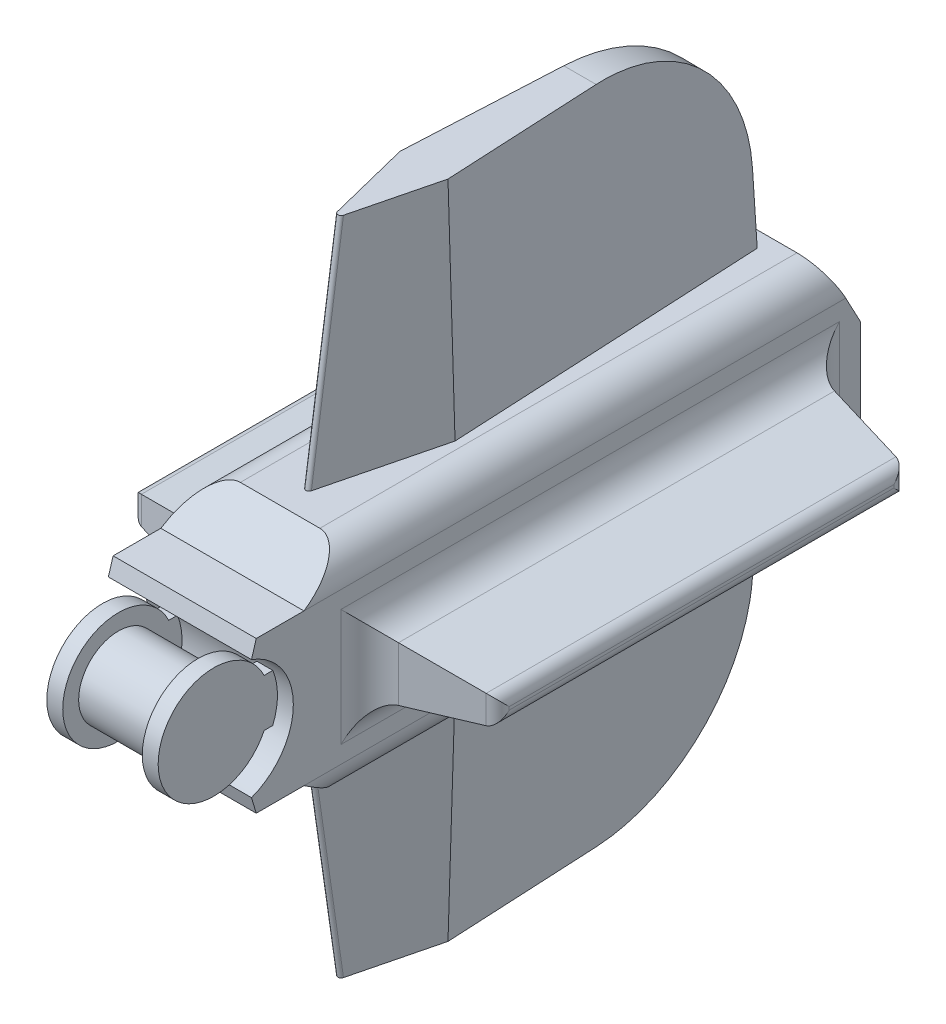
SolidWorks part; units mm, degrees
ref_plane "Front Plane" through (0, 0, 0) normal (0, 0, 1) x (1, 0, 0)
ref_plane "Top Plane" through (0, 0, 0) normal (0, 1, 0) x (1, 0, 0)
ref_plane "Right Plane" through (0, 0, 0) normal (1, 0, 0) x (0, 0, -1)
sketch "Sketch1" plane through (0, 0, 0) normal (1, 0, 0) x (0, 0, -1)
  circle A0 centre (0, 0) radius 3.175
  dimension "D1" = 6.35
extrude "Boss-Extrude1" add sketch "Sketch1" along normal mid plane 6.35
sketch "Sketch2" plane through (3.175, 0, 0) normal (1, 0, 0) x (0, 0, -1)
  circle A0 centre (0, 0) radius 4.445
  dimension "D1" = 8.89
extrude "Boss-Extrude2" add sketch "Sketch2" along normal blind 1.27
mirror "Mirror1" about plane through (0, 0, 0) normal (1, 0, 0) of "Boss-Extrude2"
sketch "Sketch3" plane through (4.445, 0, 0) normal (1, 0, 0) x (0, 0, -1)
  line L1 (0, 1.905) -> (6.35, 1.905)
  line L2 (0, 1.905) -> (0, -1.905)
  line L3 (0, -1.905) -> (6.35, -1.905)
  line L4 (6.35, 1.905) -> (6.35, -1.905)
  point P4 (0, 0)
  dimension "D1" = 3.81
  dimension "D2" = 6.35
extrude "Boss-Extrude3" add sketch "Sketch3" against normal blind 1.27
mirror "Mirror2" about plane through (0, 0, 0) normal (1, 0, 0) of "Boss-Extrude3"
sketch "Sketch4" plane through (-3.175, 0, 0) normal (1, 0, 0) x (0, 0, -1)
  line L0 (1.7375, 4.7736) -> (0, 0) construction
  line L1 (0, 0) -> (5.08, 0) construction
  line L2 (1.7375, 4.7736) -> (2.1185, 6.0436)
  line L3 (2.1185, 6.0436) -> (5.9285, 6.0436)
  line L4 (0, 0) -> (1.7375, -4.7736) construction
  line L5 (5.9285, 6.0436) -> (9.7385, 8.5836)
  line L6 (9.7385, 8.5836) -> (47.8385, 8.5836)
  line L7 (47.8385, 8.5836) -> (50.3785, 3.81)
  line L8 (50.3785, 3.81) -> (50.3785, -3.81)
  line L9 (50.3785, 0) -> (5.08, 0) construction
  line L10 (47.8385, -8.5836) -> (50.3785, -3.81)
  line L11 (9.7385, -8.5836) -> (47.8385, -8.5836)
  line L12 (5.9285, -6.0436) -> (9.7385, -8.5836)
  line L13 (2.1185, -6.0436) -> (5.9285, -6.0436)
  line L14 (1.7375, -4.7736) -> (2.1185, -6.0436)
  arc A0 (1.7375, 4.7736) -> (1.7375, -4.7736) centre (0, 0) cw
  dimension "D1" = 5.08
  dimension "D2" = 140
  dimension "D3" = 1.27
  dimension "D4" = 0.381
  dimension "D5" = 3.81
  dimension "D6" = 3.81
  dimension "D7" = 2.54
  dimension "D8" = 38.1
  dimension "D9" = 7.62
  dimension "D10" = 2.54
extrude "Boss-Extrude4" add sketch "Sketch4" against normal blind 2.54 and the other way blind 8.89
sketch "Sketch5" plane through (0, 0, -50.3785) normal (0, 0, -1) x (-1, 0, 0)
  circle A0 centre (0, 0) radius 3.175
  dimension "D1" = 6.35
extrude "Cut-Extrude1" cut sketch "Sketch5" against normal blind 12.7
fillet "Fillet1" radius 2.54 4 edges at (5.715, -8.5836, -28.7885) (-5.715, -8.5836, -28.7885) (-5.715, 8.5836, -28.7885) (5.715, 8.5836, -28.7885)
sketch "Sketch6" plane through (5.715, 0, 0) normal (1, 0, 0) x (0, 0, -1)
  line L0 (50.3785, -3.81) -> (50.3785, 3.81) construction
  line L1 (11.0085, 2.54) -> (46.5685, 2.54)
  line L2 (11.0085, 2.54) -> (11.0085, -2.54)
  line L3 (11.0085, -2.54) -> (46.5685, -2.54)
  line L4 (46.5685, 2.54) -> (46.5685, -2.54)
  point P4 (11.0085, 0)
  point P6 (50.3785, 0)
  dimension "D1" = 3.81
  dimension "D2" = 5.08
  dimension "D3" = 35.56
extrude "Boss-Extrude5" add sketch "Sketch6" along normal blind 8.89 draft 10
mirror "Mirror3" about plane through (0, 0, 0) normal (1, 0, 0) of "Boss-Extrude5"
fillet "Fillet2" radius 1.016 8 edges at (-14.605, -0.9725, -28.7885) (-14.605, 0, -45.0009) (-14.605, 0.9725, -28.7885) (-14.605, 0, -12.576) (14.605, 0.9725, -28.7885) (14.605, 0, -45.0009) (14.605, -0.9725, -28.7885) (14.605, 0, -12.576)
fillet "Fillet3" radius 2.54 8 edges at (5.715, -2.54, -28.7885) (5.715, 0, -11.0085) (5.715, 0, -46.5685) (5.715, 2.54, -28.7885) (-5.715, 0, -11.0085) (-5.715, 0, -46.5685) (-5.715, -2.54, -28.7885) (-5.715, 2.54, -28.7885)
sketch "Sketch7" plane through (0, 8.5836, 0) normal (0, 1, 0) x (1, 0, 0)
  line L0 (0, 9.7385) -> (0, 47.8385) construction
  line L1 (3.175, 9.7385) -> (-3.175, 9.7385) construction
  line L2 (3.175, 47.8385) -> (-3.175, 47.8385) construction
  line L3 (-1.27, 46.5685) -> (1.27, 46.5685)
  line L4 (1.27, 46.5685) -> (2.54, 21.1685)
  line L5 (2.54, 21.1685) -> (0, 11.0085)
  line L6 (0, 11.0085) -> (-2.54, 21.1685)
  line L7 (-2.54, 21.1685) -> (-1.27, 46.5685)
  point P8 (0, 46.5685)
  dimension "D1" = 2.54
  dimension "D2" = 1.27
  dimension "D3" = 1.27
  dimension "D4" = 2.54
  dimension "D5" = 25.4
extrude "Boss-Extrude6" add sketch "Sketch7" along normal blind 17.78 draft 2
mirror "Mirror4" about plane through (0, 0, 0) normal (0, 1, 0) of "Boss-Extrude6"
fillet "Fillet4" radius 0.254 2 edges at (0, -17.4736, -12.2885) (0, 17.4736, -12.2885)
fillet "Fillet5" radius 12.7 2 edges at (0, -26.3636, -45.9476) (0, 26.3636, -45.9476)
